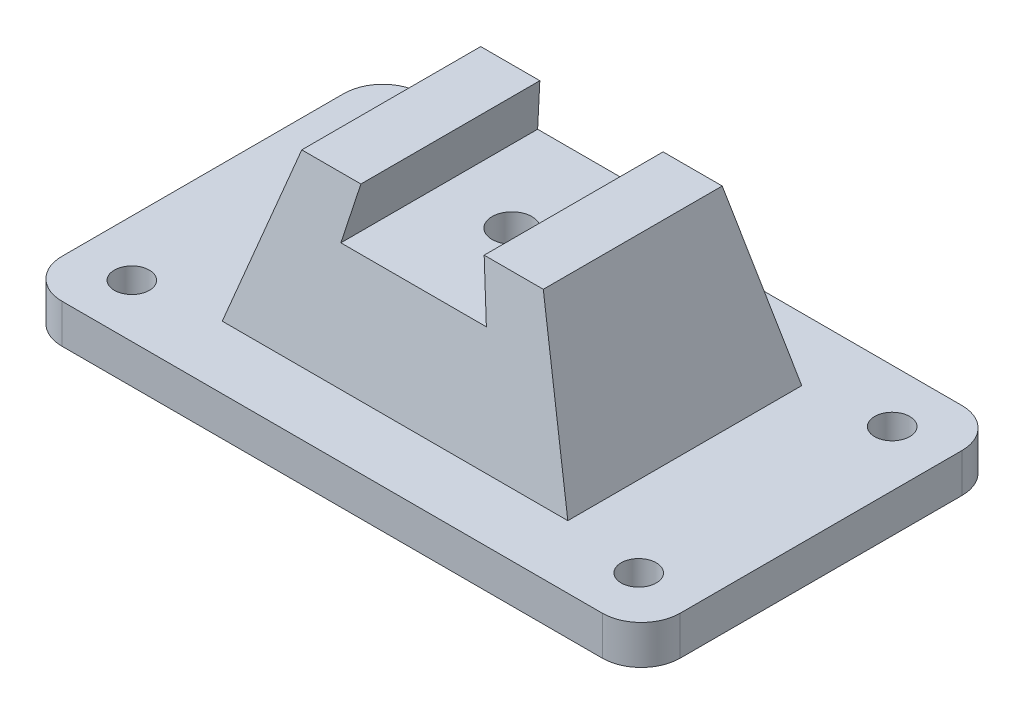
SolidWorks part; units mm, degrees
material "Rostfreier Chromstahl"
ref_plane "Ebene vorne" through (0, 0, 0) normal (0, 0, 1) x (1, 0, 0)
ref_plane "Ebene oben" through (0, 0, 0) normal (0, 1, 0) x (1, 0, 0)
ref_plane "Ebene rechts" through (0, 0, 0) normal (1, 0, 0) x (0, 0, -1)
sketch "Skizze1" plane through (0, 0, 0) normal (0, 1, 0) x (1, 0, 0)
  line L0 (0, 46.1248) -> (0, 0) construction
  line L1 (-69.2749, 46.1248) -> (69.2749, 46.1248)
  line L2 (-79.2749, 36.1248) -> (-79.2749, -36.1248)
  line L3 (-69.2749, -46.1248) -> (69.2749, -46.1248)
  line L4 (79.2749, 36.1248) -> (79.2749, -36.1248)
  line L5 (0, 0) -> (79.2749, 0) construction
  arc A0 (69.2749, 46.1248) -> (79.2749, 36.1248) centre (69.2749, 36.1248) cw
  arc A1 (69.2749, -46.1248) -> (79.2749, -36.1248) centre (69.2749, -36.1248) ccw
  arc A2 (-79.2749, -36.1248) -> (-69.2749, -46.1248) centre (-69.2749, -36.1248) ccw
  arc A3 (-69.2749, 46.1248) -> (-79.2749, 36.1248) centre (-69.2749, 36.1248) ccw
  dimension "D1" = 10
extrude "Aufsatz-Linear austragen1" add sketch "Skizze1" along normal blind 10
sketch "Skizze2" plane through (0, 0, 0) normal (0, 0, 1) x (1, 0, 0)
  line L0 (0, 10) -> (0, 51.1938) construction
  line L1 (-69.2749, 10) -> (69.2749, 10) construction
  line L2 (-30.9686, 51.1938) -> (-44.315, 10)
  line L3 (30.9686, 51.1938) -> (44.315, 10)
  line L4 (-30.9686, 51.1938) -> (30.9686, 51.1938)
  line L5 (-44.315, 10) -> (44.315, 10)
extrude "Aufsatz-Linear austragen2" add sketch "Skizze2" along normal mid plane 60
sketch "Skizze3" plane through (0, 0, 0) normal (1, 0, 0) x (0, 0, -1)
  line L0 (0, 10) -> (0, 51.1938) construction
  line L1 (-36.1248, 10) -> (36.1248, 10) construction
  line L2 (-30, 51.1938) -> (30, 51.1938) construction
  line L3 (-30, 10) -> (-22.9454, 51.1938)
  line L4 (-22.9454, 51.1938) -> (-30, 51.1938)
  line L5 (-30, 51.1938) -> (-30, 10)
  line L6 (30, 51.1938) -> (30, 10)
  line L7 (22.9454, 51.1938) -> (30, 51.1938)
  line L8 (30, 10) -> (22.9454, 51.1938)
extrude "Schnitt-Linear austragen1" cut sketch "Skizze3" against normal through all both and the other way through all
sketch "Skizze4" plane through (0, 0, 0) normal (0, 0, 1) x (1, 0, 0)
  line L0 (0, 26.9574) -> (0, 51.1938) construction
  line L1 (-30.9686, 51.1938) -> (30.9686, 51.1938) construction
  line L2 (-15.8083, 51.1938) -> (-18.6589, 37.8418)
  line L3 (15.8083, 51.1938) -> (18.6589, 37.8418)
  line L4 (-18.6589, 37.8418) -> (18.6589, 37.8418)
  line L5 (-15.8083, 51.1938) -> (15.8083, 51.1938)
extrude "Schnitt-Linear austragen2" cut sketch "Skizze4" against normal through all both and the other way through all
hole_wizard "Durchgangsloch für M81" positions "Skizze6" profile "Skizze5" hole size "M8" standard "DIN" end condition through all
sketch "Skizze6" plane through (0, 10, 0) normal (0, 1, 0) x (1, 0, 0)
  line L0 (0, 0) -> (0, 39.378) construction
  line L3 (0, 0) -> (-51.7687, 0) construction
  point P0 (-65, 32.5)
  point P13 (65, 32.5)
  point P14 (65, -32.5)
  point P15 (-65, -32.5)
  dimension "D1" = 65
  dimension "D2" = 130
sketch "Skizze5" plane through (-65, 10, -32.5) normal (1, 0, 0) x (0, 0, 1)
  line L0 (0, 0) -> (0, 10)
  line L1 (0, 10) -> (4.5, 10)
  line L2 (4.5, 10) -> (4.5, 0)
  line L5 (4.5, 0) -> (0, 0)
  line L11 (0, -6.35) -> (0, 107.95) construction
  dimension "Bohrerdurchmesser" = 9
  dimension "Bohrungstiefe" = 10
hole_wizard "M12 Gewindebohrung1" positions "Skizze8" profile "Skizze7" tap size "M12" standard "DIN" end condition through all
sketch "Skizze8" plane through (0, 37.8418, 0) normal (0, 1, 0) x (1, 0, 0)
  point P0 (0, 0)
sketch "Skizze7" plane through (0, 37.8418, 0) normal (1, 0, 0) x (0, 0, 1)
  line L0 (0, 0) -> (0, 37.8418)
  line L1 (0, 37.8418) -> (5.1, 37.8418)
  line L2 (5.1, 37.8418) -> (5.1, 0)
  line L5 (5.1, 0) -> (0, 0)
  line L11 (0, -6.35) -> (0, 107.95) construction
  dimension "Bohrerdurchmesser" = 10.2
  dimension "Bohrungstiefe" = 37.8418
cosmetic thread "Bohrungsgewinde1" parameters "D2"=12
